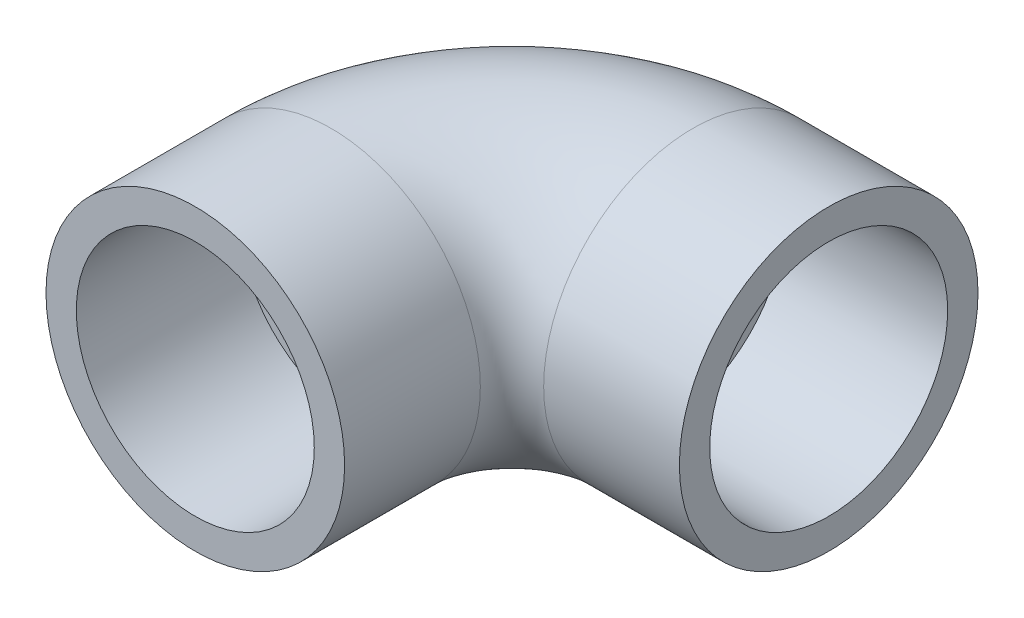
SolidWorks part; units mm, degrees
material "PVC Rigid"
ref_plane "Front Plane" through (0, 0, 0) normal (0, 0, 1) x (1, 0, 0)
ref_plane "Top Plane" through (0, 0, 0) normal (0, 1, 0) x (1, 0, 0)
ref_plane "Right Plane" through (0, 0, 0) normal (1, 0, 0) x (0, 0, -1)
sketch "Sketch1" plane through (0, 0, 0) normal (0, 0, 1) x (1, 0, 0)
  circle A0 centre (0, 0) radius 20.955
  circle A1 centre (0, 0) radius 15.621
  dimension "D1" = 41.91
  dimension "D2" = 5.334
sketch "Sketch15" plane through (0, 0, 0) normal (0, 1, 0) x (1, 0, 0)
  line L0 (0, 0) -> (0, 19.05)
  line L1 (25.4, 44.45) -> (44.45, 44.45)
  arc A0 (0, 19.05) -> (25.4, 44.45) centre (25.4, 19.05) cw
  dimension "D2" = 25.4
  dimension "D1" = 19.05
sweep "Sweep7" add profiles "Sketch1" path "Sketch15"
sketch "Sketch17" plane through (0, 0, 0) normal (0, 0, 1) x (1, 0, 0)
  circle A0 centre (0, 0) radius 16.7005
  dimension "D1" = 33.401
extrude "Cut-Extrude1" cut sketch "Sketch17" against normal blind 22.86
sketch "Sketch18" plane through (44.45, 0, 0) normal (1, 0, 0) x (0, 0, -1)
  circle A0 centre (44.45, 0) radius 16.7005
  dimension "D1" = 33.401
extrude "Cut-Extrude2" cut sketch "Sketch18" against normal blind 22.86
